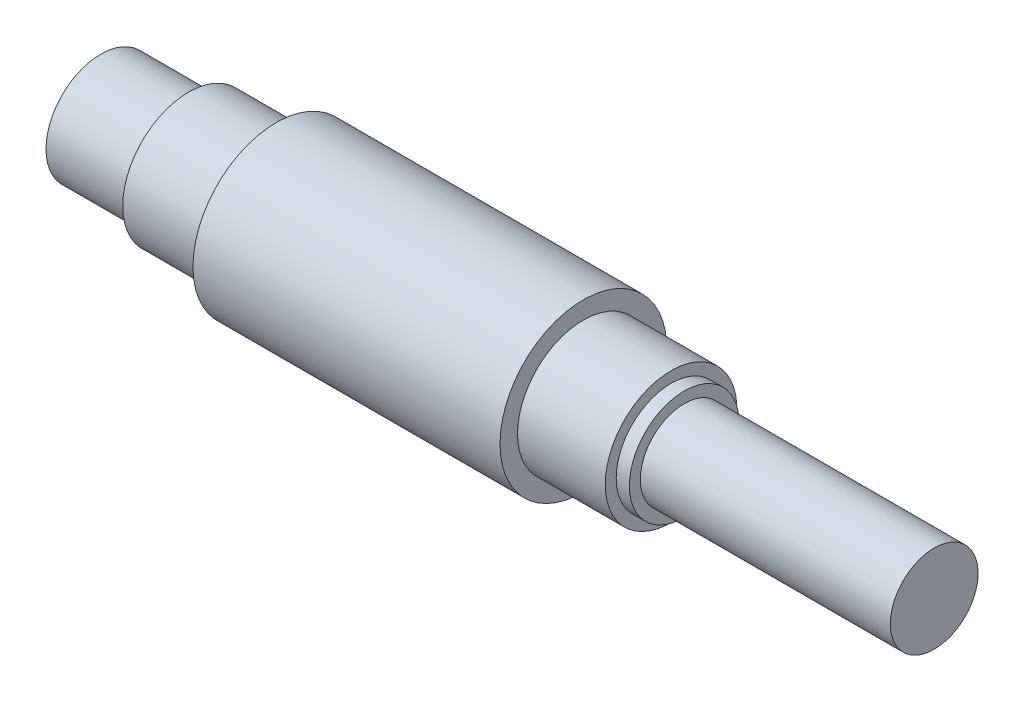
SolidWorks part; units mm, degrees
ref_plane "Спереди" through (0, 0, 0) normal (0, 0, 1) x (1, 0, 0)
ref_plane "Сверху" through (0, 0, 0) normal (0, 1, 0) x (1, 0, 0)
ref_plane "Справа" through (0, 0, 0) normal (1, 0, 0) x (0, 0, -1)
other "Configuration Table"
sketch "Эскиз2" plane through (0, 0, 0) normal (0, 0, 1) x (1, 0, 0)
  line L0 (0, 0) -> (236.0157, 0) construction
  line L1 (0, 12.5) -> (20, 12.5)
  line L2 (20, 15) -> (40, 15)
  line L3 (40, 19) -> (110, 19)
  line L4 (110, 15) -> (130, 15)
  line L5 (130, 12.5) -> (133, 12.5)
  line L6 (133, 10) -> (190, 10)
  line L7 (0, 12.5) -> (0, 0)
  line L8 (190, 10) -> (190, 0)
  line L9 (20, 15) -> (20, 12.5)
  line L10 (40, 19) -> (40, 15)
  line L11 (110, 19) -> (110, 15)
  line L12 (130, 15) -> (130, 12.5)
  line L13 (133, 12.5) -> (133, 10)
  line L14 (0, 0) -> (190, 0)
  dimension "D1" = 20
  dimension "D2" = 20
  dimension "D3" = 70
  dimension "D4" = 20
  dimension "D5" = 3
  dimension "D6" = 57
  dimension "D7" = 25
  dimension "D8" = 30
  dimension "D9" = 38
  dimension "D10" = 30
  dimension "D11" = 25
  dimension "D12" = 20
revolve "Повернуть11" add sketch "Эскиз2" angle 360 about L0
sketch "Эскиз3" plane through (0, 0, 0) normal (-1, 0, 0) x (0, 0, 1)
  line L1 (0, 0) -> (-6.2593, 0)
  line L2 (0, 0) -> (0, 22.6109)
  line L3 (0, 22.6109) -> (-6.2593, 22.6109)
  line L4 (-6.2593, 0) -> (-6.2593, 22.6109)
